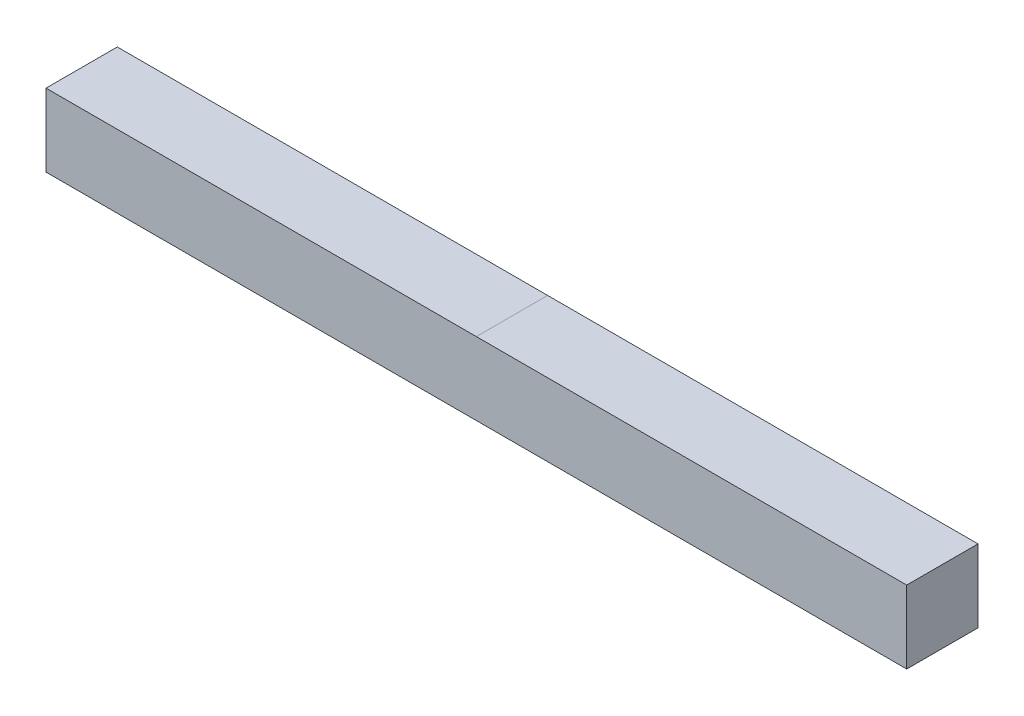
SolidWorks part; units mm, degrees
material "Acrylic (Medium-high impact)"
ref_plane "Front Plane" through (0, 0, 0) normal (0, 0, 1) x (1, 0, 0)
ref_plane "Top Plane" through (0, 0, 0) normal (0, 1, 0) x (1, 0, 0)
ref_plane "Right Plane" through (0, 0, 0) normal (1, 0, 0) x (0, 0, -1)
sketch "Sketch1" plane through (0, 0, 0) normal (1, 0, 0) x (0, 0, -1)
  line L1 (-6.3119, -6.4389) -> (6.3119, -6.4389)
  line L2 (-6.3119, -6.4389) -> (-6.3119, 6.4389)
  line L3 (-6.3119, 6.4389) -> (6.3119, 6.4389)
  line L4 (6.3119, -6.4389) -> (6.3119, 6.4389)
  line L5 (-6.3119, -6.4389) -> (6.3119, 6.4389) construction
  line L6 (-6.3119, 6.4389) -> (6.3119, -6.4389) construction
  point P0 (0, 0)
  dimension "D1" = 12.8778
  dimension "D2" = 12.6238
extrude "Boss-Extrude1" add sketch "Sketch1" along normal mid plane 152.4 contours L3 L4 L1 L2
ref_plane "Plane1" through (63.5, 0, 0) normal (1, 0, 0) x (0, 0, -1)
ref_plane "Plane2" through (-63.5, 0, 0) normal (1, 0, 0) x (0, 0, -1)
split line "Split Line1"
split line "Split Line3"
